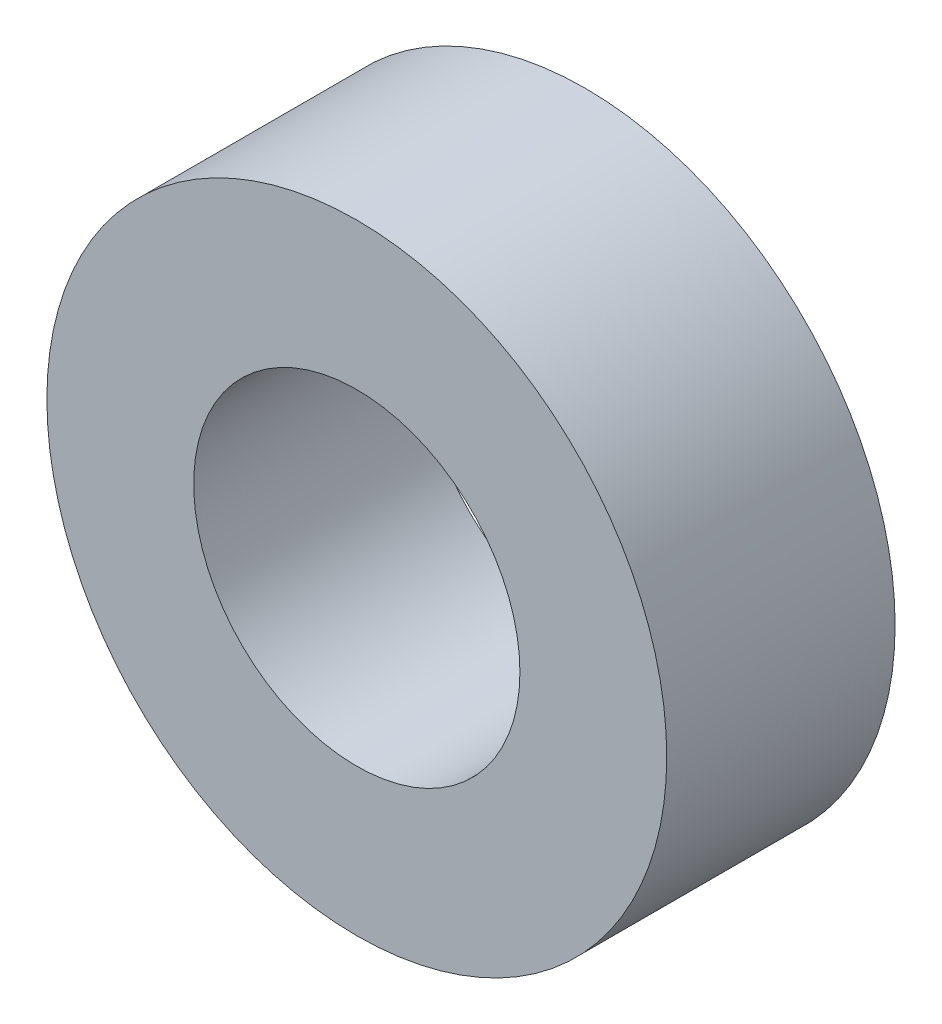
SolidWorks part; units mm, degrees
ref_plane "Plan de face" through (0, 0, 0) normal (0, 0, 1) x (1, 0, 0)
ref_plane "Plan de dessus" through (0, 0, 0) normal (0, 1, 0) x (1, 0, 0)
ref_plane "Plan de droite" through (0, 0, 0) normal (1, 0, 0) x (0, 0, -1)
sketch "Esquisse1" plane through (0, 0, 0) normal (0, 0, 1) x (1, 0, 0)
  circle A0 centre (0, 0) radius 5
  circle A1 centre (0, 0) radius 9.5
extrude "Extrusion1" add sketch "Esquisse1" along normal blind 7
